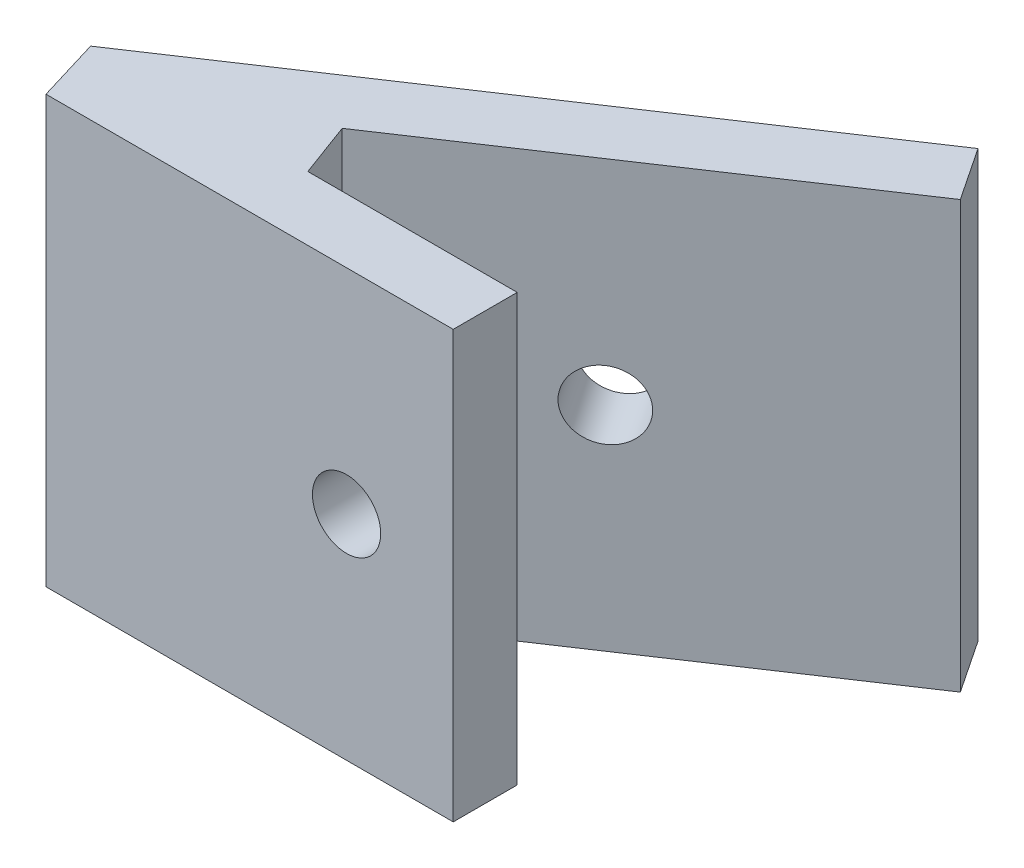
SolidWorks part; units mm, degrees
ref_plane "前视基准面" through (0, 0, 0) normal (0, 0, 1) x (1, 0, 0)
ref_plane "上视基准面" through (0, 0, 0) normal (0, 1, 0) x (1, 0, 0)
ref_plane "右视基准面" through (0, 0, 0) normal (1, 0, 0) x (0, 0, -1)
sketch "草图1" plane through (0, 0, 0) normal (0, 1, 0) x (1, 0, 0)
  line L0 (3.9013, 80.3308) -> (22.993, 80.3308)
  line L1 (22.993, 80.3308) -> (22.993, 83.3308)
  line L2 (22.993, 83.3308) -> (13.1761, 83.3308)
  line L4 (2.993, 83.3308) -> (27.9545, 99.9718)
  line L7 (27.9545, 99.9718) -> (29.611, 97.487)
  line L10 (29.611, 97.487) -> (12.2298, 85.8903)
  line L12 (2.993, 83.3308) -> (3.9013, 80.3308)
  line L13 (13.1761, 83.3308) -> (12.2298, 85.8903)
  point P0 (8.3935, 83.3308)
  dimension "D1" = 3
  dimension "D2" = 20
  dimension "D3" = 19.0917
  dimension "D4" = 30
extrude "凸台-拉伸1" add sketch "草图1" along normal blind 20
sketch "草图4" plane through (0, 0, -83.3308) normal (0, 0, -1) x (-1, 0, 0)
  line L0 (-22.993, 10) -> (-2.993, 10) construction
  line L1 (-22.993, 20) -> (-22.993, 0) construction
  line L2 (-2.993, 20) -> (-2.993, 0) construction
  line L3 (-2.993, 20) -> (-2.993, 0) construction
  circle A1 centre (-17.993, 10) radius 1.6
  dimension "D1" = 15
extrude "切除-拉伸1" cut sketch "草图4" against normal through all
sketch "草图5" plane through (-37.5394, 0, -56.3092) normal (-0.5547, 0, -0.8321) x (-0.8321, 0, 0.5547)
  line L0 (-78.7139, 10) -> (-48.7139, 10) construction
  line L6 (-78.7139, 20) -> (-78.7139, 0) construction
  line L7 (-48.7139, 20) -> (-48.7139, 0) construction
  circle A1 centre (-66.7139, 10) radius 1.6
  dimension "D1" = 12
extrude "切除-拉伸2" cut sketch "草图5" against normal up to next
